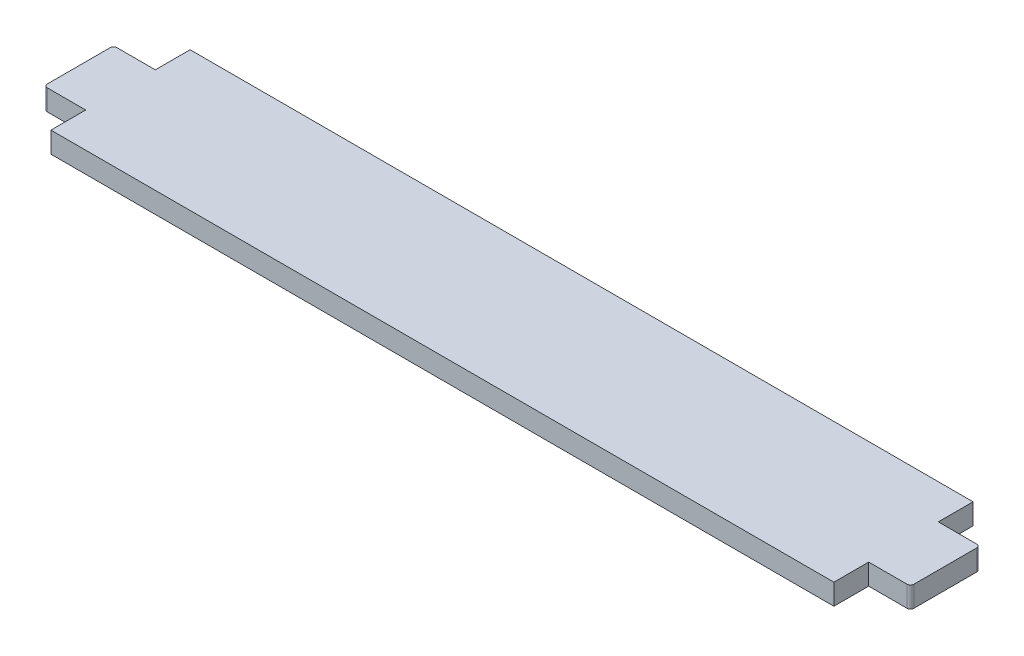
SolidWorks part; units mm, degrees
ref_plane "Спереди" through (0, 0, 0) normal (0, 0, 1) x (1, 0, 0)
ref_plane "Сверху" through (0, 0, 0) normal (0, 1, 0) x (1, 0, 0)
ref_plane "Справа" through (0, 0, 0) normal (1, 0, 0) x (0, 0, -1)
sketch "Эскиз1" plane through (0, 0, 0) normal (0, 1, 0) x (1, 0, 0)
  line L0 (0, 0) -> (0, 33.2741) construction
  line L1 (-56.25, 10) -> (56.25, 10)
  line L2 (-56.25, 10) -> (-56.25, -10)
  line L3 (-56.25, -10) -> (56.25, -10)
  line L4 (56.25, 10) -> (56.25, -10)
  line L5 (-56.25, 10) -> (56.25, -10) construction
  line L6 (-56.25, -10) -> (56.25, 10) construction
  line L7 (56.25, 5) -> (62.25, 5)
  line L8 (56.25, 5) -> (56.25, -5)
  line L9 (56.25, -5) -> (62.25, -5)
  line L10 (62.25, 5) -> (62.25, -5)
  line L11 (56.25, 5) -> (62.25, -5) construction
  line L12 (56.25, -5) -> (62.25, 5) construction
  line L13 (-56.25, -5) -> (-62.25, 5) construction
  line L14 (-56.25, 5) -> (-62.25, -5) construction
  line L15 (-62.25, 5) -> (-62.25, -5)
  line L16 (-56.25, -5) -> (-62.25, -5)
  line L17 (-56.25, 5) -> (-56.25, -5)
  line L18 (-56.25, 5) -> (-62.25, 5)
  point P0 (0, 0)
  point P6 (59.25, 0)
  point P17 (-59.25, 0)
  dimension "D1" = 20
  dimension "D2" = 6
  dimension "D3" = 10
  dimension "D4" = 112.5
extrude "Бобышка-Вытянуть1" add sketch "Эскиз1" along normal blind 3 contours L2 L18 L15 L16 | L4 L1 L2 L3 | L10 L7 L4 L9
fillet "Скругление1" radius 0.5 4 edges at (-62.25, 1.5, -5) (-62.25, 1.5, 5) (62.25, 1.5, -5) (62.25, 1.5, 5)
